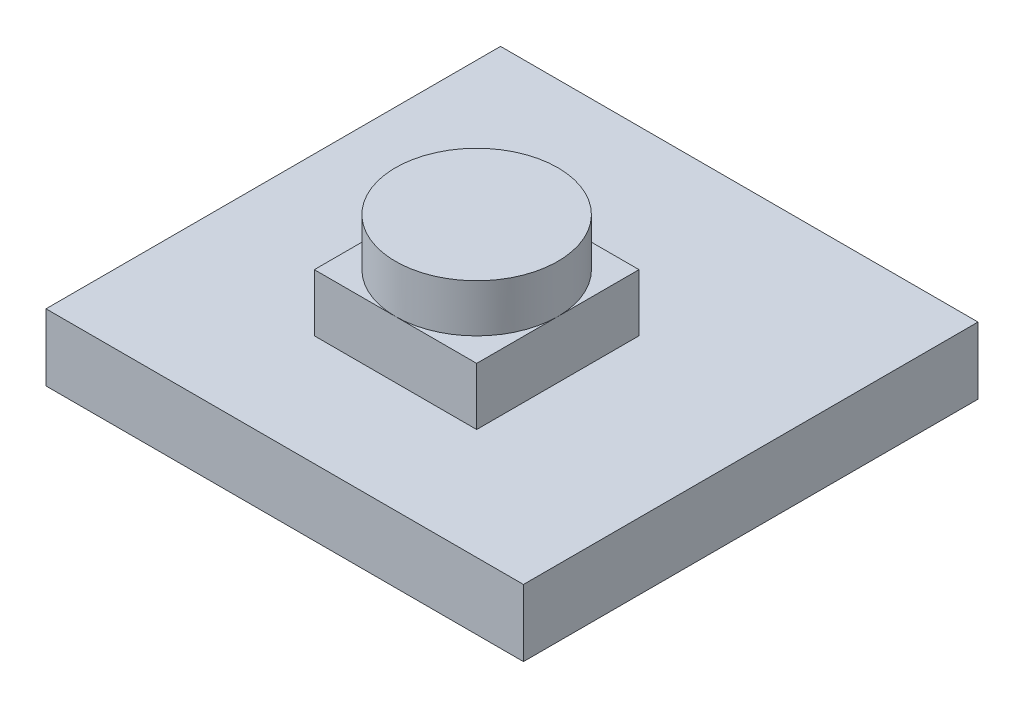
SolidWorks part; units mm, degrees
ref_plane "Front Plane" through (0, 0, 0) normal (0, 0, 1) x (1, 0, 0)
ref_plane "Top Plane" through (0, 0, 0) normal (0, 1, 0) x (1, 0, 0)
ref_plane "Right Plane" through (0, 0, 0) normal (1, 0, 0) x (0, 0, -1)
sketch "Sketch1" plane through (0, 0, 0) normal (0, 1, 0) x (1, 0, 0)
  line L1 (-12.5, -11.9) -> (12.5, -11.9)
  line L2 (-12.5, -11.9) -> (-12.5, 11.9)
  line L3 (-12.5, 11.9) -> (12.5, 11.9)
  line L4 (12.5, -11.9) -> (12.5, 11.9)
  line L5 (-12.5, -11.9) -> (12.5, 11.9) construction
  line L6 (-12.5, 11.9) -> (12.5, -11.9) construction
  point P0 (0, 0)
  dimension "D1" = 25
  dimension "D2" = 23.8
extrude "Boss-Extrude1" add sketch "Sketch1" along normal blind 3.5
sketch "Sketch2" plane through (0, 3.5, 0) normal (0, 1, 0) x (1, 0, 0)
  line L0 (-12.5, -11.9) -> (12.5, -11.9) construction
  line L1 (-4.25, -6.1) -> (4.25, -6.1)
  line L2 (-4.25, -6.1) -> (-4.25, 2.4)
  line L3 (-4.25, 2.4) -> (4.25, 2.4)
  line L4 (4.25, -6.1) -> (4.25, 2.4)
  line L5 (-4.25, -6.1) -> (4.25, 2.4) construction
  line L6 (-4.25, 2.4) -> (4.25, -6.1) construction
  line L8 (0, 0) -> (0, -1.85) construction
  dimension "D1" = 14.3
  dimension "D3" = 8.5
  dimension "D4" = 8.5
extrude "Boss-Extrude2" add sketch "Sketch2" along normal blind 6.5 from surface at -3.5 starting at face at (0, 0, 0)
sketch "Sketch3" plane through (0, 6.5, 0) normal (0, 1, 0) x (1, 0, 0)
  circle A0 centre (0, -1.85) radius 4.25
extrude "Boss-Extrude3" add sketch "Sketch3" along normal blind 9 from surface at -6.5 starting at face at (0, 0, 0)
